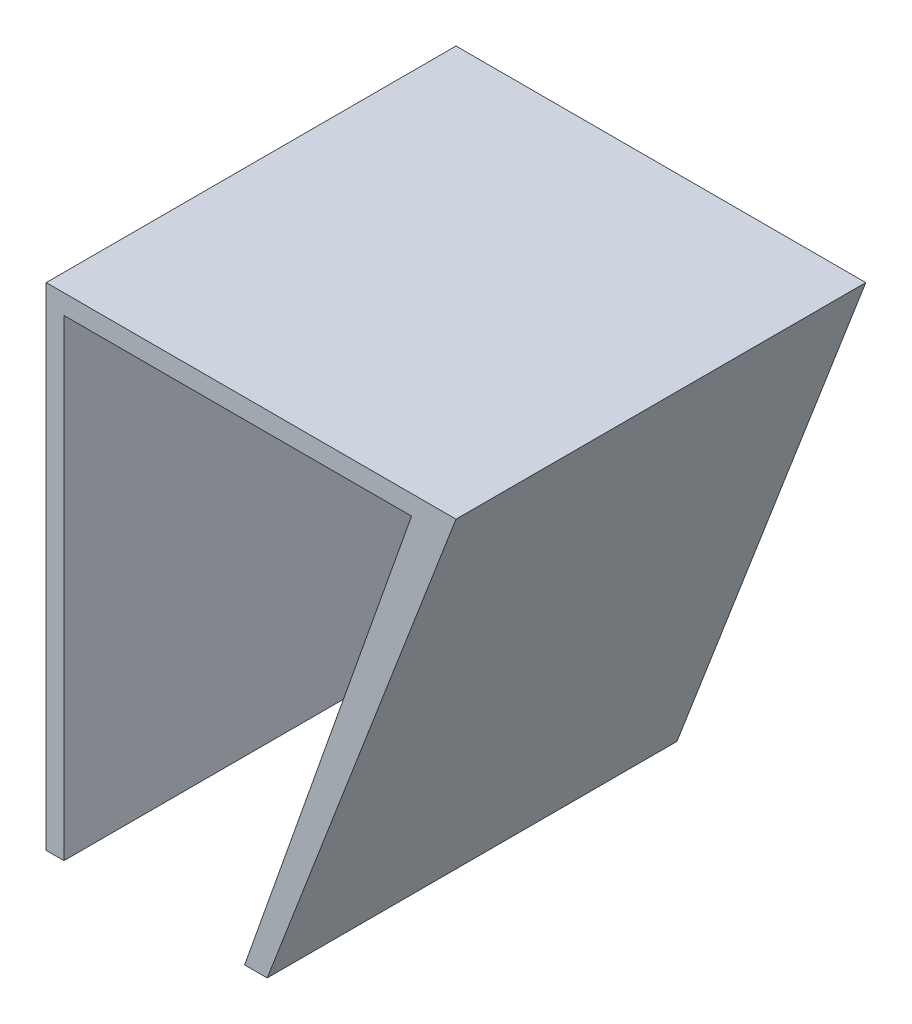
SolidWorks part; units mm, degrees
ref_plane "Front Plane" through (0, 0, 0) normal (0, 0, 1) x (1, 0, 0)
ref_plane "Top Plane" through (0, 0, 0) normal (0, 1, 0) x (1, 0, 0)
ref_plane "Right Plane" through (0, 0, 0) normal (1, 0, 0) x (0, 0, -1)
sketch "Sketch1" plane through (0, 0, 0) normal (0, 0, 1) x (1, 0, 0)
  line L0 (0, 0) -> (0, 45.72)
  line L1 (0, 45.72) -> (38.1, 45.72)
  line L2 (38.1, 45.72) -> (20.545, 0)
  line L3 (20.545, 0) -> (18.4463, 0)
  line L4 (1.6497, 43.9002) -> (1.6497, 0)
  line L5 (1.6497, 43.9002) -> (33.9667, 43.9002)
  line L6 (33.9667, 43.9002) -> (18.4463, 0)
  line L7 (1.6497, 0) -> (0, 0)
  point P4 (30.3676, 37.7518)
  point P8 (0, 0)
  point P11 (1.6497, 44.2001)
  point P12 (0, 0)
  point P13 (0, 0)
  point P14 (0, 0)
  point P15 (0, 0)
  point P16 (0, 45.72)
  point P17 (33.9667, 43.9002)
  point P18 (20.545, 0)
  dimension "D1" = 45.72
  dimension "D2" = 45.72
  dimension "D3" = 38.1
  dimension "D4" = 70.53
extrude "Boss-Extrude4" add sketch "Sketch1" along normal blind 38.1
